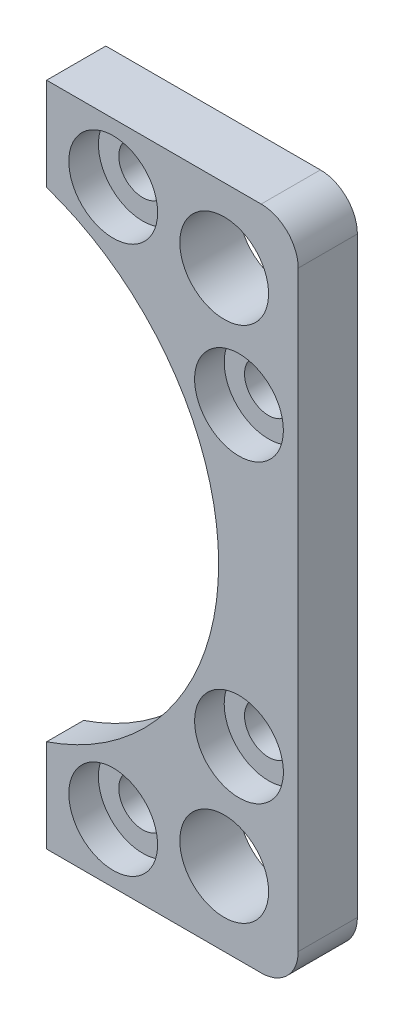
SolidWorks part; units mm, degrees
ref_plane "Front Plane" through (0, 0, 0) normal (0, 0, 1) x (1, 0, 0)
ref_plane "Top Plane" through (0, 0, 0) normal (0, 1, 0) x (1, 0, 0)
ref_plane "Right Plane" through (0, 0, 0) normal (1, 0, 0) x (0, 0, -1)
sketch "Sketch1" plane through (0, 0, 0) normal (0, 0, 1) x (1, 0, 0)
  line L0 (-35, 45) -> (-35, 35) construction
  line L1 (-45, -45) -> (45, -45) construction
  line L2 (-45, -45) -> (-45, 45) construction
  line L3 (-45, 45) -> (45, 45) construction
  line L4 (45, -45) -> (45, 45) construction
  line L5 (-45, -45) -> (45, 45) construction
  line L6 (-45, 45) -> (45, -45) construction
  line L7 (-35, 35) -> (-45, 35) construction
  line L8 (-1000, 0) -> (49000, 0) construction
  line L9 (0, -1000) -> (0, 49000) construction
  line L10 (-11, 45) -> (-11, 32.4355) construction
  line L11 (-11, -45) -> (-11, -32.4355) construction
  line L12 (-11, 45) -> (-45, 45) construction
  line L13 (-45, 45) -> (-45, -45) construction
  line L14 (-45, -45) -> (-11, -45) construction
  line L15 (45, -45) -> (11, -45)
  line L16 (11, -45) -> (11, -32.4355)
  line L17 (45, 45) -> (45, -45)
  line L18 (11, 45) -> (45, 45)
  line L19 (11, 45) -> (11, 32.4355)
  arc A0 (-11, 32.4355) -> (-11, -32.4355) centre (0, 0) ccw construction
  circle A1 centre (-35, 35) radius 6 construction
  circle A2 centre (-35, -35) radius 6 construction
  circle A3 centre (-37, 20) radius 3.25 construction
  circle A4 centre (-37, -20) radius 3.25 construction
  circle A5 centre (-20, 37) radius 3.25 construction
  circle A6 centre (-20, -37) radius 3.25 construction
  circle A7 centre (20, 37) radius 3.25
  circle A8 centre (35, 35) radius 6
  circle A9 centre (37, 20) radius 3.25
  circle A10 centre (37, -20) radius 3.25
  circle A11 centre (35, -35) radius 6
  circle A12 centre (20, -37) radius 3.25
  arc A13 (11, 32.4355) -> (11, -32.4355) centre (0, 0) cw
  point P0 (0, 0)
  dimension "D2" = 68.5
  dimension "D4" = 12
  dimension "D6" = 6.5
  dimension "D1" = 90
  dimension "D3" = 10
  dimension "D5" = 8
  dimension "D7" = 20
  dimension "D8" = 8
  dimension "D9" = 20
  dimension "D10" = 34
extrude "Boss-Extrude1" add sketch "Sketch1" along normal mid plane 8
sketch "Sketch3" plane through (0, 0, -4) normal (0, 0, -1) x (-1, 0, 0)
  circle A0 centre (0, 0) radius 36
  dimension "D1" = 72
extrude "Cut-Extrude2" cut sketch "Sketch3" against normal blind 3
fillet "Fillet1" radius 5 2 edges at (45, -45, 0) (45, 45, 0)
sketch "Sketch4" plane through (0, 0, 4) normal (0, 0, 1) x (1, 0, 0)
  line L0 (-1000, 0) -> (49000, 0) construction
  circle A0 centre (20, 37) radius 6
  circle A1 centre (37, 20) radius 6
  circle A2 centre (20, -37) radius 6
  circle A3 centre (37, -20) radius 6
  dimension "D1" = 12
extrude "Cut-Extrude3" cut sketch "Sketch4" against normal blind 4
